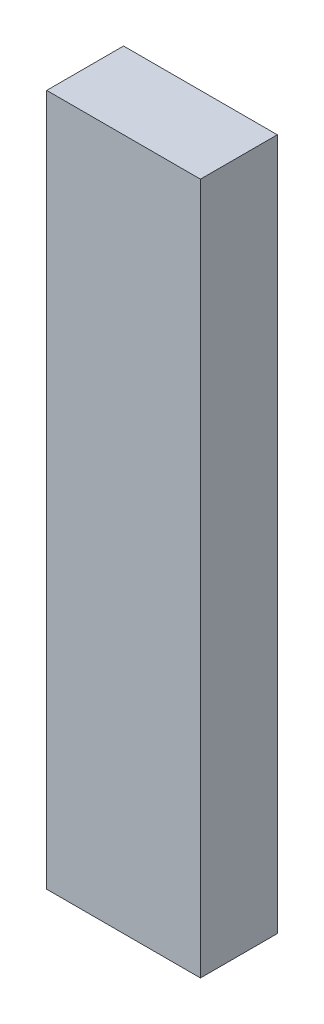
SolidWorks part; units mm, degrees
ref_plane "Plan de face" through (0, 0, 0) normal (0, 0, 1) x (1, 0, 0)
ref_plane "Plan de dessus" through (0, 0, 0) normal (0, 1, 0) x (1, 0, 0)
ref_plane "Plan de droite" through (0, 0, 0) normal (1, 0, 0) x (0, 0, -1)
sketch "Esquisse1" plane through (0, 0, 0) normal (0, 0, 1) x (1, 0, 0)
  line L0 (0, 0) -> (10, 0)
  line L1 (10, 0) -> (10, 45)
  line L2 (10, 45) -> (0, 45)
  line L3 (0, 45) -> (0, 0)
extrude "Extrusion1" add sketch "Esquisse1" along normal blind 5
